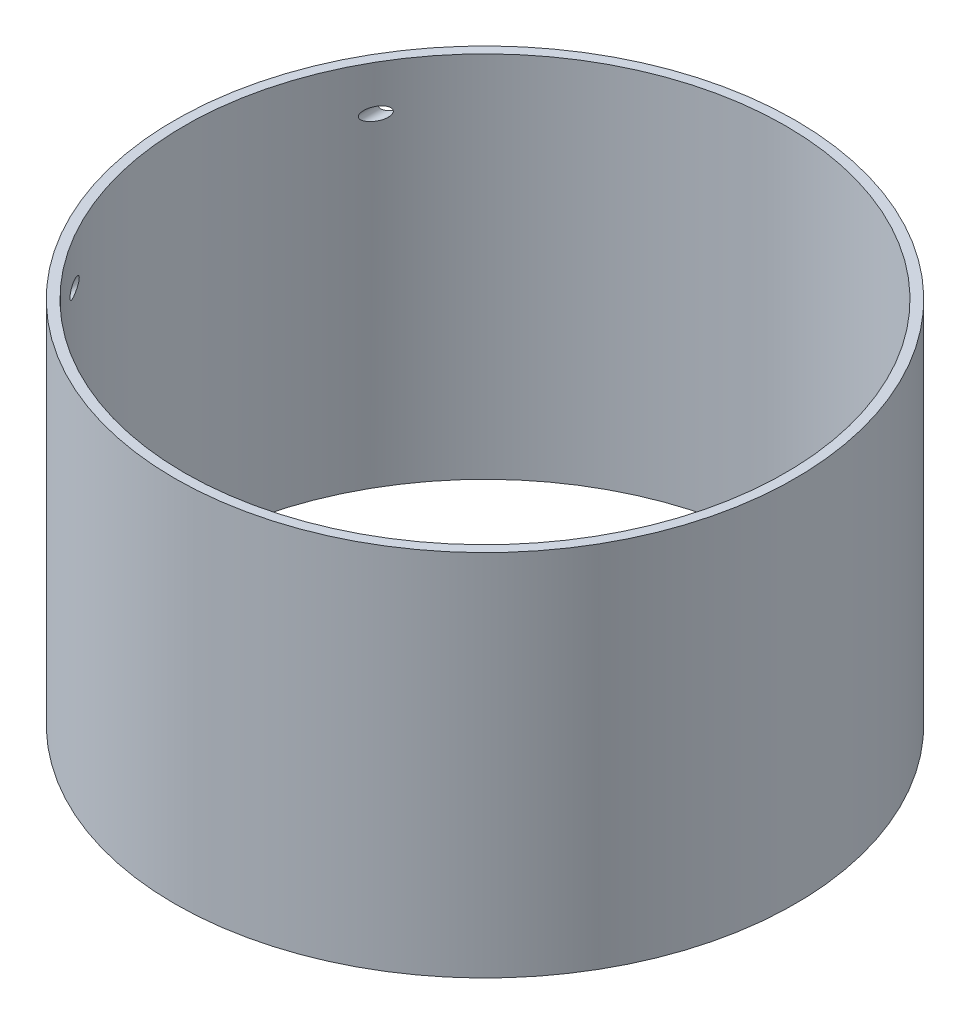
SolidWorks part; units mm, degrees
ref_plane "Front Plane" through (0, 0, 0) normal (0, 0, 1) x (1, 0, 0)
ref_plane "Top Plane" through (0, 0, 0) normal (0, 1, 0) x (1, 0, 0)
ref_plane "Right Plane" through (0, 0, 0) normal (1, 0, 0) x (0, 0, -1)
sketch "Sketch1" plane through (0, 0, 0) normal (0, 1, 0) x (1, 0, 0)
  circle A0 centre (0, 0) radius 101.6
  circle A1 centre (0, 0) radius 95.25
  dimension "D1" = 203.2
  dimension "D2" = 190.5
extrude "Boss-Extrude1" add sketch "Sketch1" along normal blind 25.4
sketch "Sketch2" plane through (0, 0, 0) normal (0, 0, 1) x (1, 0, 0)
  circle A0 centre (0, 12.7) radius 3.175
  dimension "D1" = 6.35
extrude "Cut-Extrude1" cut sketch "Sketch2" against normal through all and the other way through all
sketch "Sketch3" plane through (0, 0, 0) normal (1, 0, 0) x (0, 0, -1)
  circle A0 centre (0, 12.7) radius 1.5875
  dimension "D1" = 3.175
extrude "Cut-Extrude3" [suppressed] cut sketch "Sketch3" against normal through all
sketch "Sketch4" plane through (0, 0, 0) normal (1, 0, 0) x (0, 0, -1)
  line L0 (0, 0) -> (0, 72.5565) construction
pattern_circular "CirPattern1" [suppressed] count 24 over 360 about axis through (0, 0, 0) along (0, 1, 0)
sketch "Sketch5" plane through (0, 25.4, 0) normal (0, 1, 0) x (1, 0, 0)
  circle A0 centre (0, 0) radius 98.425
  circle A1 centre (0, 0) radius 101.6
extrude "Boss-Extrude2" add sketch "Sketch5" along normal blind 146.05
sketch "Sketch6" plane through (0, 0, 0) normal (0, -1, 0) x (1, 0, 0)
  circle A0 centre (0, 0) radius 101.6
  circle A1 centre (0, 0) radius 98.425
extrude "Boss-Extrude3" [suppressed] add sketch "Sketch6" along normal blind 133.35
ref_plane "Plane1" through (0, 0, 101.6) normal (0, 0, 1) x (1, 0, 0)
sketch "Sketch9" plane through (0, 0, 101.6) normal (0, 0, 1) x (1, 0, 0)
  line L0 (-101.6, 0) -> (101.6, 0) construction
  line L1 (0, 0) -> (0, 72.5565) construction
  circle A0 centre (-85.075, 156.8) radius 2.1
  dimension "D1" = 156.8
  dimension "D2" = 85.075
extrude "Cut-Extrude5" cut sketch "Sketch9" against normal through all
sketch "Sketch10" plane through (0, 0, 0) normal (0, -1, 0) x (-1, 0, 0)
  circle A0 centre (0, 0) radius 101.6
extrude "Cut-Extrude6" cut sketch "Sketch10" against normal blind 50.8
